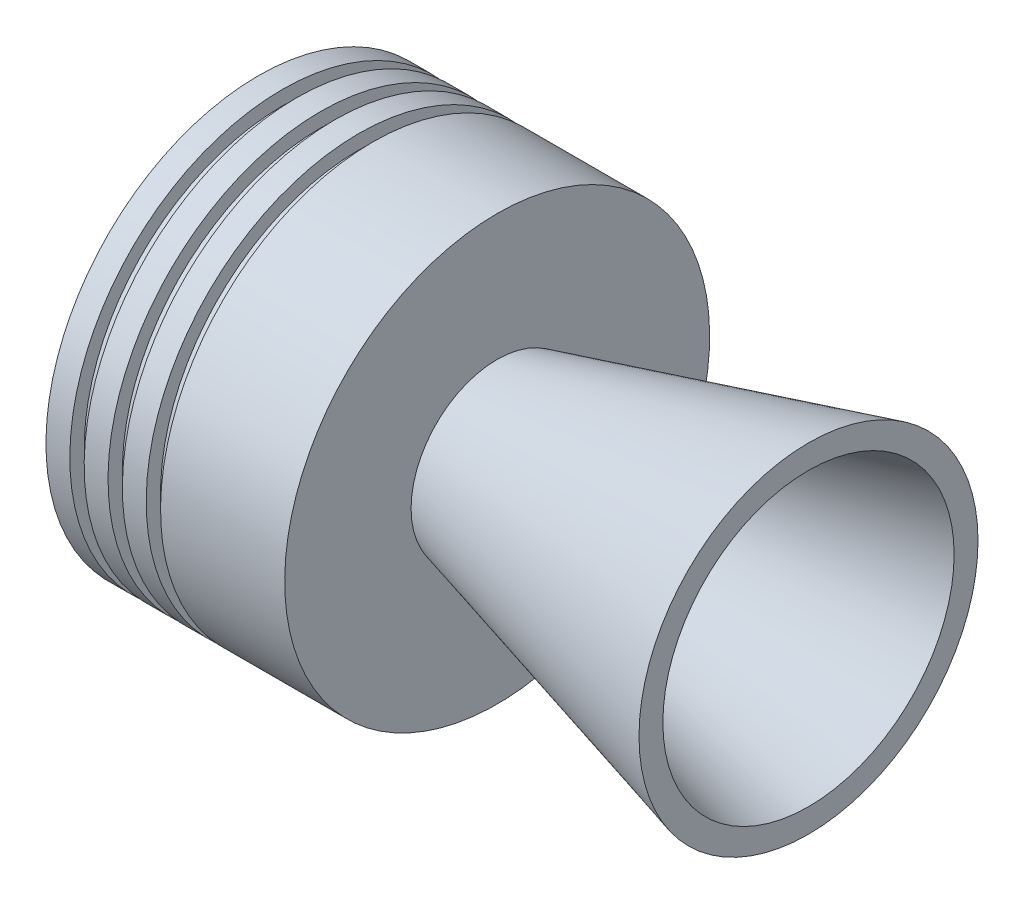
SolidWorks part; units mm, degrees
material "AISI 4130 Steel, annealed at 865C"
ref_plane "Front Plane" through (0, 0, 0) normal (0, 0, 1) x (1, 0, 0)
ref_plane "Top Plane" through (0, 0, 0) normal (0, 1, 0) x (1, 0, 0)
ref_plane "Right Plane" through (0, 0, 0) normal (1, 0, 0) x (0, 0, -1)
sketch "Sketch1" plane through (0, 0, 0) normal (0, 0, 1) x (1, 0, 0)
  line L0 (0, 0) -> (-126.4, 0) construction
  line L1 (-82.1051, 11.5) -> (0, 33.5)
  line L2 (-82.1051, 11.5) -> (-83.1051, 11.5)
  line L3 (-83.1051, 11.5) -> (-126.4, 36.4963)
  line L4 (-126.4, 36.4963) -> (-126.4, 44.4963)
  line L5 (-126.4, 44.4963) -> (-121.4, 44.4963)
  line L6 (-121.4, 44.4963) -> (-121.4, 41.4963)
  line L7 (-121.4, 41.4963) -> (-118.4, 41.4963)
  line L8 (-118.4, 41.4963) -> (-118.4, 44.4963)
  line L9 (-118.4, 44.4963) -> (-113.4, 44.4963)
  line L10 (-113.4, 44.4963) -> (-113.4, 41.4963)
  line L11 (-113.4, 41.4963) -> (-110.4, 41.4963)
  line L12 (-110.4, 41.4963) -> (-110.4, 44.4963)
  line L13 (-110.4, 44.4963) -> (-105.4, 44.4963)
  line L14 (-105.4, 44.4963) -> (-105.4, 41.4963)
  line L15 (-105.4, 41.4963) -> (-102.4, 41.4963)
  line L16 (-102.4, 41.4963) -> (-102.4, 44.4963)
  line L17 (-102.4, 44.4963) -> (-76.4, 44.4963)
  line L18 (-76.4, 44.4963) -> (-76.4, 18.0287)
  line L20 (0, 38.5) -> (0, 33.5)
  line L21 (-76.4, 18.0287) -> (0, 38.5)
  dimension "D1" = 126.4
  dimension "D2" = 11.5
  dimension "D3" = 15
  dimension "D4" = 33.5
  dimension "D5" = 1
  dimension "D6" = 30
  dimension "D7" = 8
  dimension "D8" = 5
  dimension "D9" = 3
  dimension "D10" = 3
  dimension "D11" = 5
  dimension "D12" = 3
  dimension "D13" = 5
  dimension "D14" = 3
  dimension "D15" = 26
  dimension "D16" = 5
revolve "Revolve1" add sketch "Sketch1" angle 360 about L0
sketch "Sketch2" plane through (0, 0, 0) normal (0, 0, 1) x (1, 0, 0)
  line L0 (0, 0) -> (-76.4, 0) construction
  line L1 (-76.4, -44.4963) -> (-76.4, 44.4963) construction
  line L2 (-11.1962, 0) -> (-11.1962, 35.5)
  line L3 (0, 38.5) -> (-76.4, 18.0287) construction
  line L4 (-11.1962, 35.5) -> (-11.1962, 56.2719)
  line L5 (-11.1962, 56.2719) -> (14.5313, 56.2719)
  line L6 (14.5313, 56.2719) -> (14.5313, 0)
  line L7 (14.5313, 0) -> (-11.1962, 0)
  dimension "D1" = 35.5
revolve "Cut-Revolve1" cut sketch "Sketch2" angle 360 about L0
